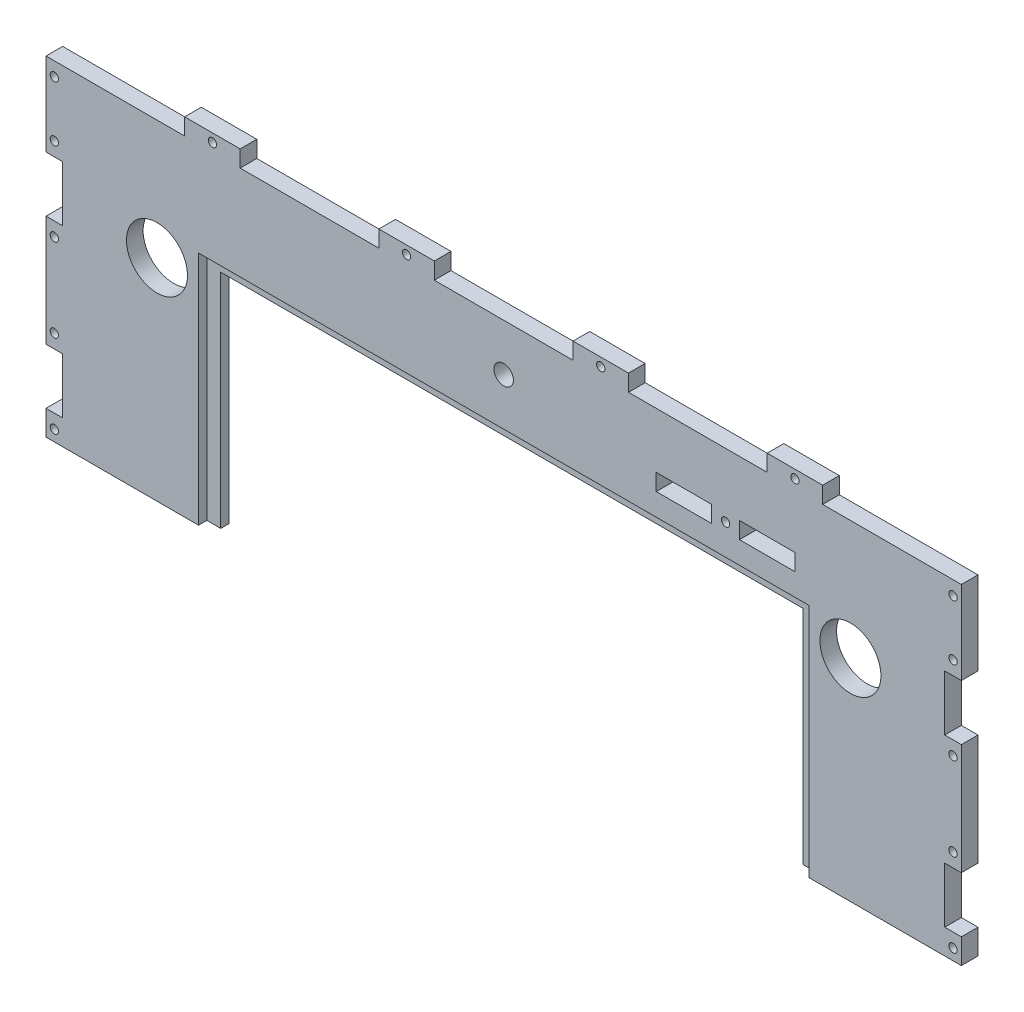
SolidWorks part; units mm, degrees
ref_plane "Plan de face" through (0, 0, 0) normal (0, 0, 1) x (1, 0, 0)
ref_plane "Plan de dessus" through (0, 0, 0) normal (0, 1, 0) x (1, 0, 0)
ref_plane "Plan de droite" through (0, 0, 0) normal (1, 0, 0) x (0, 0, -1)
sketch "Esquisse1" plane through (0, 0, 0) normal (0, 0, 1) x (1, 0, 0)
  line L0 (97.3951, 0) -> (-118.5049, 0) construction
  line L1 (-165, 119) -> (165, 119)
  line L2 (-165, 119) -> (-165, -119)
  line L3 (-165, -119) -> (165, -119)
  line L4 (165, 119) -> (165, -119)
  line L5 (0, 79.3588) -> (0, -79.3588) construction
  line L6 (-92.5, -55) -> (-77.5, -55)
  line L7 (-92.5, -55) -> (-92.5, -61)
  line L8 (-92.5, -61) -> (-77.5, -61)
  line L9 (-77.5, -55) -> (-77.5, -61)
  line L10 (-7.5, -55) -> (7.5, -55)
  line L11 (-7.5, -55) -> (-7.5, -61)
  line L12 (-7.5, -61) -> (7.5, -61)
  line L13 (7.5, -55) -> (7.5, -61)
  line L14 (77.5, -55) -> (92.5, -55)
  line L15 (77.5, -55) -> (77.5, -61)
  line L16 (77.5, -61) -> (92.5, -61)
  line L17 (92.5, -55) -> (92.5, -61)
  line L18 (-225.3679, 76) -> (203.1013, 76) construction
  line L19 (55, 99) -> (75, 99)
  line L20 (55, 99) -> (55, 93)
  line L21 (55, 93) -> (75, 93)
  line L22 (75, 99) -> (75, 93)
  line L23 (85, 99) -> (105, 99)
  line L24 (85, 99) -> (85, 93)
  line L25 (85, 93) -> (105, 93)
  line L26 (105, 99) -> (105, 93)
  circle A0 centre (-125, 76) radius 11
  circle A1 centre (125, 76) radius 11
  dimension "D23" = 22
  dimension "D24" = 22
  dimension "D1" = 238
  dimension "D2" = 330
  dimension "D3" = 165
  dimension "D4" = 119
  dimension "D5" = 15
  dimension "D6" = 6
  dimension "D7" = 6
  dimension "D8" = 15
  dimension "D9" = 6
  dimension "D10" = 15
  dimension "D11" = 70
  dimension "D12" = 70
  dimension "D13" = 58
  dimension "D14" = 72.5
  dimension "D15" = 6
  dimension "D16" = 20
  dimension "D17" = 20
  dimension "D18" = 6
  dimension "D19" = 10
  dimension "D20" = 60
  dimension "D21" = 20
  dimension "D22" = 20
  dimension "D25" = 40
  dimension "D26" = 40
  dimension "D27" = 195
extrude "Boss.-Extru.1" add sketch "Esquisse1" along normal blind 6
sketch "Esquisse2" plane through (0, 0, 6) normal (0, 0, 1) x (1, 0, 0)
  line L0 (243.146, 0) -> (-260.0003, 0) construction
  line L1 (0, 180.4713) -> (0, -129.6072) construction
  line L2 (165, 119) -> (-165, 119) construction
  line L3 (-115, 119) -> (-95, 119)
  line L4 (-115, 119) -> (-115, 125)
  line L5 (-115, 125) -> (-95, 125)
  line L6 (-95, 119) -> (-95, 125)
  line L7 (-165, 119) -> (-165, -119) construction
  line L8 (-45, 119) -> (-25, 119)
  line L9 (-45, 119) -> (-45, 125)
  line L10 (-45, 125) -> (-25, 125)
  line L11 (-25, 119) -> (-25, 125)
  line L12 (25, 119) -> (25, 125)
  line L13 (45, 125) -> (25, 125)
  line L14 (45, 119) -> (45, 125)
  line L15 (45, 119) -> (25, 119)
  line L16 (95, 119) -> (95, 125)
  line L17 (115, 125) -> (95, 125)
  line L18 (115, 119) -> (115, 125)
  line L19 (115, 119) -> (95, 119)
  line L20 (-115, 119) -> (-95, 119)
  line L21 (-115, 119) -> (-115, 125)
  line L22 (-115, 125) -> (-95, 125)
  line L23 (-95, 119) -> (-95, 125)
  line L24 (-45, 119) -> (-25, 119)
  line L25 (-45, 119) -> (-45, 125)
  line L26 (-45, 125) -> (-25, 125)
  line L27 (-25, 119) -> (-25, 125)
  line L28 (25, 119) -> (25, 125)
  line L29 (45, 125) -> (25, 125)
  line L30 (45, 119) -> (45, 125)
  line L31 (45, 119) -> (25, 119)
  line L32 (95, 119) -> (95, 125)
  line L33 (115, 125) -> (95, 125)
  line L34 (115, 119) -> (115, 125)
  line L35 (115, 119) -> (95, 119)
  line L36 (115, -119) -> (95, -119)
  line L37 (115, -119) -> (115, -125)
  line L38 (115, -125) -> (95, -125)
  line L39 (95, -119) -> (95, -125)
  line L40 (45, -119) -> (25, -119)
  line L41 (45, -119) -> (45, -125)
  line L42 (45, -125) -> (25, -125)
  line L43 (25, -119) -> (25, -125)
  line L44 (-25, -119) -> (-25, -125)
  line L45 (-45, -125) -> (-25, -125)
  line L46 (-45, -119) -> (-45, -125)
  line L47 (-45, -119) -> (-25, -119)
  line L48 (-95, -119) -> (-95, -125)
  line L49 (-115, -125) -> (-95, -125)
  line L50 (-115, -119) -> (-115, -125)
  line L51 (-115, -119) -> (-95, -119)
  line L52 (115, -119) -> (95, -119)
  line L53 (115, -119) -> (115, -125)
  line L54 (115, -125) -> (95, -125)
  line L55 (95, -119) -> (95, -125)
  line L56 (45, -119) -> (25, -119)
  line L57 (45, -119) -> (45, -125)
  line L58 (45, -125) -> (25, -125)
  line L59 (25, -119) -> (25, -125)
  line L60 (-25, -119) -> (-25, -125)
  line L61 (-45, -125) -> (-25, -125)
  line L62 (-45, -119) -> (-45, -125)
  line L63 (-45, -119) -> (-25, -119)
  line L64 (-95, -119) -> (-95, -125)
  line L65 (-115, -125) -> (-95, -125)
  line L66 (-115, -119) -> (-115, -125)
  line L67 (-115, -119) -> (-95, -119)
  line M9 (-165, -119) -> (165, -119)
  line M11 (165, 119) -> (-165, 119)
  dimension "D1" = 6
  dimension "D2" = 6
  dimension "D3" = 20
  dimension "D4" = 20
  dimension "D5" = 50
  dimension "D6" = 50
extrude "Boss.-Extru.2" add sketch "Esquisse2" against normal blind 6 contours L6 L5 L4 M11 | L11 L10 L9 M11 | L14 L13 L12 M11 | L18 L17 L16 M11 | L39 L38 L37 M9 | L43 L42 L41 M9 | L46 L45 L44 M9 | L50 L49 L48 M9
sketch "Esquisse3" plane through (0, 0, 6) normal (0, 0, 1) x (1, 0, 0)
  line L0 (-165, 119) -> (-165, -119) construction
  line L1 (-165, 69) -> (-159, 69)
  line L2 (-165, 69) -> (-165, 89)
  line L3 (-165, 89) -> (-159, 89)
  line L4 (-159, 69) -> (-159, 89)
  line L5 (234.1368, 0) -> (-337.9213, 0) construction
  line L6 (-165, 29) -> (-159, 29)
  line L7 (-165, 29) -> (-165, 9)
  line L8 (-165, 9) -> (-159, 9)
  line L9 (-159, 29) -> (-159, 9)
  line L10 (0, 279.7488) -> (0, -188.1201) construction
  line L11 (-115, 119) -> (-165, 119) construction
  line L12 (-159, -29) -> (-159, -9)
  line L13 (-165, -9) -> (-159, -9)
  line L14 (-165, -29) -> (-165, -9)
  line L15 (-165, -29) -> (-159, -29)
  line L16 (-159, -69) -> (-159, -89)
  line L17 (-165, -89) -> (-159, -89)
  line L18 (-165, -69) -> (-165, -89)
  line L19 (-165, -69) -> (-159, -69)
  line L20 (165, -69) -> (159, -69)
  line L21 (165, -69) -> (165, -89)
  line L22 (165, -89) -> (159, -89)
  line L23 (159, -69) -> (159, -89)
  line L24 (165, -29) -> (159, -29)
  line L25 (165, -29) -> (165, -9)
  line L26 (165, -9) -> (159, -9)
  line L27 (159, -29) -> (159, -9)
  line L28 (159, 29) -> (159, 9)
  line L29 (165, 9) -> (159, 9)
  line L30 (165, 29) -> (165, 9)
  line L31 (165, 29) -> (159, 29)
  line L32 (159, 69) -> (159, 89)
  line L33 (165, 89) -> (159, 89)
  line L34 (165, 69) -> (165, 89)
  line L35 (165, 69) -> (159, 69)
  line L36 (153, -119) -> (153, -109)
  line L37 (-165, -119) -> (-153, -119)
  line L38 (-165, -119) -> (-165, -109)
  line L39 (-165, -109) -> (-153, -109)
  line L40 (-153, -119) -> (-153, -109)
  line L41 (165, -109) -> (153, -109)
  line L42 (165, -119) -> (165, -109)
  line L43 (165, -119) -> (153, -119)
  dimension "D1" = 40
  dimension "D2" = 6
  dimension "D3" = 6
  dimension "D4" = 20
  dimension "D5" = 20
  dimension "D6" = 30
  dimension "D7" = 12
  dimension "D8" = 10
extrude "Enlèv. mat.-Extru.1" cut sketch "Esquisse3" against normal blind 6
sketch "Esquisse4" plane through (0, 0, 6) normal (0, 0, 1) x (1, 0, 0)
  line L0 (-162, 122) -> (-162, -131.0602) construction
  line L1 (0, 158.5579) -> (0, -182.4489) construction
  line L2 (-115, 119) -> (-165, 119) construction
  line L3 (-106.4439, -58) -> (117.3944, -58) construction
  line L4 (-159, 89) -> (-165, 89) construction
  line L5 (-165, 119) -> (-165, 89) construction
  line L6 (-165, 69) -> (-159, 69) construction
  line L7 (-159, 29) -> (-165, 29) construction
  line L8 (-165, 9) -> (-159, 9) construction
  line L9 (-159, -9) -> (-165, -9) construction
  line L10 (-92.5, -55) -> (-92.5, -61) construction
  line L11 (-77.5, -61) -> (-77.5, -55) construction
  line L12 (-165, -29) -> (-159, -29) construction
  line L13 (-159, -69) -> (-165, -69) construction
  line L14 (-165, -89) -> (-159, -89) construction
  line L15 (-7.5, -55) -> (-7.5, -61) construction
  line L16 (162, 122) -> (162, -131.0602) construction
  line L17 (116.5184, 96) -> (43.4816, 96) construction
  line L18 (-126.5544, 122) -> (2.7821, 122) construction
  line L19 (-45, 119) -> (-95, 119) construction
  line L20 (-45, 119) -> (-45, 125) construction
  line L21 (75, 93) -> (75, 99) construction
  line L23 (55, 93) -> (75, 93) construction
  circle A0 centre (-162, 114) radius 1.5
  circle A1 centre (-162, 94) radius 1.5
  circle A2 centre (-162, 64) radius 1.5
  circle A3 centre (-162, 34) radius 1.5
  circle A4 centre (-162, 4) radius 1.5
  circle A5 centre (-105, 122) radius 1.5
  circle A6 centre (-162, -4) radius 1.5
  circle A7 centre (-162, -34) radius 1.5
  circle A8 centre (-162, -64) radius 1.5
  circle A9 centre (-162, -94) radius 1.5
  circle A10 centre (-97.5, -58) radius 1.5
  circle A11 centre (-72.5, -58) radius 1.5
  circle A12 centre (162, -94) radius 1.5
  circle A13 centre (162, -64) radius 1.5
  circle A14 centre (162, -34) radius 1.5
  circle A15 centre (162, -4) radius 1.5
  circle A16 centre (80, 96) radius 1.5
  circle A17 centre (162, 4) radius 1.5
  circle A18 centre (162, 34) radius 1.5
  circle A19 centre (162, 64) radius 1.5
  circle A20 centre (162, 94) radius 1.5
  circle A21 centre (162, 114) radius 1.5
  circle A22 centre (-12.5, -58) radius 1.5
  circle A23 centre (12.5, -58) radius 1.5
  circle A24 centre (72.5, -58) radius 1.5
  circle A25 centre (97.5, -58) radius 1.5
  circle A26 centre (-35, 122) radius 1.5
  circle A27 centre (35, 122) radius 1.5
  circle A28 centre (105, 122) radius 1.5
  dimension "D1" = 3
  dimension "D2" = 3
  dimension "D3" = 3
  dimension "D4" = 3
  dimension "D5" = 3
  dimension "D6" = 3
  dimension "D7" = 3
  dimension "D8" = 3
  dimension "D9" = 3
  dimension "D10" = 3
  dimension "D11" = 3
  dimension "D12" = 5
  dimension "D13" = 5
  dimension "D15" = 5
  dimension "D16" = 5
  dimension "D17" = 5
  dimension "D19" = 3
  dimension "D20" = 5
  dimension "D21" = 5
  dimension "D23" = 3
  dimension "D24" = 3
  dimension "D25" = 5
  dimension "D26" = 5
  dimension "D27" = 5
  dimension "D28" = 10
  dimension "D29" = 3
  dimension "D30" = 5
  dimension "D31" = 3
  dimension "D33" = 10
  dimension "D14" = 3
  dimension "D18" = 5
  dimension "D22" = 5
  dimension "D32" = 3
extrude "Enlèv. mat.-Extru.2" cut sketch "Esquisse4" against normal blind 6
sketch "Esquisse5" plane through (0, 0, 6) normal (0, 0, 1) x (1, 0, 0)
  line L1 (-200.0968, 0) -> (223.5072, 0)
  line L2 (-200.0968, 0) -> (-200.0968, -150.3561)
  line L3 (-200.0968, -150.3561) -> (223.5072, -150.3561)
  line L4 (223.5072, 0) -> (223.5072, -150.3561)
extrude "Enlèv. mat.-Extru.3" cut sketch "Esquisse5" against normal blind 6
sketch "Esquisse6" plane through (0, 0, 6) normal (0, 0, 1) x (1, 0, 0)
  line L0 (-165, 69) -> (-165, 29) construction
  line L2 (165, 0) -> (-165, 0) construction
  text T0 "SUDRIABOTIK" font "Century Gothic" height in points 72
  dimension "D1" = 83.5
  dimension "D2" = 29.5
extrude "Enlèv. mat.-Extru.4" cut sketch "Esquisse6" against normal blind 6
sketch "Esquisse7" plane through (0, 0, 6) normal (0, 0, 1) x (1, 0, 0)
  line L0 (-42.8696, 29.5) -> (-48.7731, 29.5) construction
  line L1 (-44.3875, 29.5) -> (-45.9701, 29.5)
  line L2 (-44.3875, 29.5) -> (-44.3875, 31.4538)
  line L3 (-44.3875, 31.4538) -> (-45.9701, 31.4538)
  line L4 (-45.9701, 29.5) -> (-45.9701, 31.4538)
  line L5 (-47.0635, 31.4538) -> (-44.8768, 31.4538) construction
  line L6 (-23.9531, 46.5962) -> (-27.525, 46.5962) construction
  line L7 (-45.1788, 46.5937) -> (-43.5909, 46.5937)
  line L8 (-45.1788, 46.5937) -> (-45.1788, 48.5305)
  line L9 (-45.1788, 48.5305) -> (-43.5909, 48.5305)
  line L10 (-43.5909, 46.5937) -> (-43.5909, 48.5305)
  line L11 (-26.3286, 46.5962) -> (-25.4223, 46.5962)
  line L12 (-26.3286, 46.5962) -> (-26.3286, 48.55)
  line L13 (-26.3286, 48.55) -> (-25.4223, 48.55)
  line L14 (-25.4223, 46.5962) -> (-25.4223, 48.55)
  line L15 (-27.525, 46.5962) -> (-27.525, 40.2462) construction
  line L16 (-27.525, 43.4212) -> (-29.2346, 43.4212)
  line L17 (-27.525, 43.4212) -> (-27.525, 42.4505)
  line L18 (-27.525, 42.4505) -> (-29.2346, 42.4505)
  line L19 (-29.2346, 43.4212) -> (-29.2346, 42.4505)
  line L20 (-29.2346, 29.5) -> (-29.2346, 48.55) construction
  line L21 (-2.2967, 37.5596) -> (4.5112, 37.5596) construction
  line L22 (0.6712, 37.5596) -> (1.8879, 37.5596)
  line L23 (0.6712, 37.5596) -> (0.6712, 35.6058)
  line L24 (0.6712, 35.6058) -> (1.8879, 35.6058)
  line L25 (1.8879, 37.5596) -> (1.8879, 35.6058)
  line L26 (5.4118, 35.6058) -> (-3.224, 35.6058) construction
  line L27 (15.2154, 46.5962) -> (15.2154, 40.4904) construction
  line L28 (15.2154, 43.5433) -> (13.5058, 43.5433)
  line L29 (15.2154, 43.5433) -> (15.2154, 40.4904)
  line L30 (15.2154, 40.4904) -> (13.5058, 40.4904)
  line L31 (13.5058, 43.5433) -> (13.5058, 40.4904)
  line L32 (13.5058, 29.5) -> (13.5058, 48.55) construction
  line L33 (15.2154, 38.5365) -> (15.2154, 31.4538) construction
  line L34 (15.2154, 32.964) -> (13.5058, 32.964)
  line L35 (15.2154, 32.964) -> (15.2154, 35.6058)
  line L36 (15.2154, 35.6058) -> (13.5058, 35.6058)
  line L37 (13.5058, 32.964) -> (13.5058, 35.6058)
  line L39 (29.3929, 39.4529) -> (27.6822, 39.4529)
  line L40 (29.3929, 39.4529) -> (29.3929, 38.5462)
  line L41 (29.3929, 38.5462) -> (27.6822, 38.5462)
  line L42 (27.6822, 39.4529) -> (27.6822, 38.5462)
  line L43 (45.9733, 39.5873) -> (47.6814, 39.5873)
  line L44 (45.9733, 39.5873) -> (45.9733, 38.4818)
  line L45 (45.9733, 38.4818) -> (47.6814, 38.4818)
  line L46 (47.6814, 39.5873) -> (47.6814, 38.4818)
  spline S0 degree 3 poles (-39.8701, 46.0619) (-40.0299, 46.1061) (-40.3695, 46.2) (-40.9238, 46.3025) (-41.5477, 46.3928) (-42.2438, 46.4694) (-43.0115, 46.5243) (-43.8512, 46.5655) (-44.7634, 46.5933) (-45.3958, 46.5952) (-45.724, 46.5962) knots 0 0 0 0 0.084319 0.179285 0.286583 0.405111 0.535593 0.67819 0.832976 1 1 1 1 construction
  spline S1 degree 3 poles (-44.9264, 48.55) (-44.5919, 48.5476) (-43.9455, 48.5429) (-43.0114, 48.5134) (-42.1472, 48.4612) (-41.3556, 48.3852) (-40.6345, 48.2918) (-39.986, 48.1748) (-39.4066, 48.0366) (-39.0502, 47.9188) (-38.8817, 47.8631) knots 0 0 0 0 0.164289 0.317406 0.458844 0.589367 0.707831 0.81577 0.91288 1 1 1 1 construction
  spline S2 degree 3 poles (37.6465, 47.0846) (37.4657, 47.0824) (37.1058, 47.078) (36.5709, 47.0202) (36.043, 46.9379) (35.522, 46.8204) (35.0101, 46.6604) (34.5026, 46.4762) (34.004, 46.2518) (33.516, 45.9983) (33.0429, 45.7178) (32.5966, 45.4077) (32.1757, 45.0754) (31.7814, 44.72) (31.4148, 44.3398) (31.0687, 43.9406) (30.757, 43.5108) (30.4714, 43.0623) (30.2157, 42.5955) (29.9884, 42.1154) (29.8024, 41.618) (29.6508, 41.1088) (29.5251, 40.5886) (29.4454, 40.0534) (29.387, 39.5058) (29.3829, 39.1358) (29.3808, 38.9487) knots 0 0 0 0 0.042023 0.083645 0.124984 0.166247 0.207702 0.249631 0.291742 0.334743 0.37746 0.419556 0.461044 0.502096 0.542891 0.583801 0.624864 0.666225 0.707399 0.748557 0.789655 0.83074 0.87207 0.913993 0.956498 1 1 1 1 construction
  spline S3 degree 3 poles (37.7151, 29.0115) (37.3699, 29.02) (36.6894, 29.0366) (35.6905, 29.1791) (34.731, 29.4019) (33.8138, 29.7204) (32.9384, 30.132) (32.1029, 30.6338) (31.3109, 31.2293) (30.5688, 31.9051) (29.8898, 32.6409) (29.2979, 33.4292) (28.7959, 34.2546) (28.3857, 35.1195) (28.0609, 36.0196) (27.8394, 36.9609) (27.6961, 37.9381) (27.6795, 38.6034) (27.6712, 38.941) knots 0 0 0 0 0.065819 0.129747 0.192072 0.253459 0.31457 0.37628 0.439026 0.503267 0.567493 0.629705 0.691 0.751452 0.812004 0.87315 0.935635 1 1 1 1 construction
  spline S4 degree 3 poles (45.9885, 39.0364) (45.9863, 39.221) (45.9819, 39.5872) (45.9246, 40.1286) (45.8424, 40.6579) (45.7239, 41.1732) (45.5713, 41.6744) (45.383, 42.1613) (45.161, 42.6355) (44.9062, 43.0959) (44.6199, 43.5378) (44.3069, 43.9601) (43.962, 44.3551) (43.595, 44.7325) (43.1968, 45.0842) (42.7691, 45.4104) (42.3171, 45.7188) (41.8385, 45.9971) (41.3446, 46.2541) (40.8378, 46.4743) (40.3238, 46.6613) (39.804, 46.8209) (39.274, 46.9374) (38.7373, 47.0203) (38.1947, 47.078) (37.8298, 47.0824) (37.6465, 47.0846) knots 0 0 0 0 0.042915 0.08513 0.126473 0.167453 0.207976 0.248249 0.28875 0.32967 0.370537 0.411129 0.451819 0.492406 0.533486 0.575263 0.617441 0.660672 0.70394 0.746868 0.789079 0.831104 0.873238 0.915166 0.957381 1 1 1 1 construction
  spline S5 degree 3 poles (47.6981, 39.0326) (47.6896, 38.69) (47.673, 38.0145) (47.5306, 37.0231) (47.3072, 36.0702) (46.9883, 35.1571) (46.5788, 34.2831) (46.0745, 33.4504) (45.4805, 32.6588) (44.8044, 31.9169) (44.0675, 31.2365) (43.277, 30.6437) (42.4508, 30.1336) (41.5783, 29.7265) (40.6709, 29.4012) (39.7207, 29.1794) (38.732, 29.0363) (38.0578, 29.0199) (37.7151, 29.0115) knots 0 0 0 0 0.065227 0.128569 0.19032 0.251378 0.312388 0.373789 0.436431 0.500567 0.564687 0.627136 0.688455 0.749246 0.810155 0.871671 0.934773 1 1 1 1 construction
  spline S6 degree 3 poles (29.3808, 38.9487) (29.3877, 38.6735) (29.4014, 38.1321) (29.5209, 37.3387) (29.705, 36.5762) (29.9763, 35.8488) (30.3157, 35.1502) (30.7349, 34.4867) (31.2316, 33.858) (31.7959, 33.2686) (32.4127, 32.7306) (33.0676, 32.2584) (33.7537, 31.8588) (34.4727, 31.5333) (35.2208, 31.2753) (36.0029, 31.0986) (36.8136, 30.9822) (37.3662, 30.9711) (37.6465, 30.9654) knots 0 0 0 0 0.064504 0.126899 0.187747 0.24815 0.308586 0.369583 0.431827 0.49618 0.560668 0.623504 0.68526 0.746537 0.808327 0.870486 0.934317 1 1 1 1 construction
  spline S7 degree 3 poles (37.6465, 30.9654) (37.8348, 30.968) (38.2084, 30.9731) (38.7641, 31.0248) (39.3098, 31.1077) (39.8447, 31.2271) (40.3682, 31.3765) (40.8825, 31.5539) (41.3822, 31.7754) (41.8735, 32.02) (42.3437, 32.2989) (42.7926, 32.5985) (43.2089, 32.9303) (43.6029, 33.2804) (43.9709, 33.6557) (44.3106, 34.0559) (44.6208, 34.4834) (44.9063, 34.9313) (45.1611, 35.3993) (45.383, 35.8812) (45.5713, 36.3756) (45.7233, 36.8834) (45.8425, 37.4035) (45.9245, 37.9367) (45.982, 38.4819) (45.9863, 38.8506) (45.9885, 39.0364) knots 0 0 0 0 0.043633 0.086538 0.129177 0.171436 0.213416 0.255266 0.297369 0.339941 0.382347 0.423953 0.464871 0.505572 0.546003 0.586568 0.627065 0.668271 0.709549 0.750428 0.791096 0.832027 0.873136 0.914611 0.956956 1 1 1 1 construction
extrude "Boss.-Extru.5" add sketch "Esquisse7" against normal blind 6
sketch "Esquisse8" plane through (0, 0, 6) normal (0, 0, 1) x (1, 0, 0)
  line L0 (165, 0) -> (-165, 0) construction
  line L1 (-105.0044, 0) -> (104.9956, 0)
  line L2 (-105.0044, 0) -> (-105.0044, 80)
  line L3 (-105.0044, 80) -> (104.9956, 80)
  line L4 (104.9956, 0) -> (104.9956, 80)
  dimension "D1" = 210
  dimension "D2" = 80
  dimension "D3" = 23.96
extrude "Enlèv. mat.-Extru.5" cut sketch "Esquisse8" against normal blind 6 contours L2 L3 L4 L1
sketch "Esquisse11" plane through (0, 0, 6) normal (0, 0, 1) x (1, 0, 0)
  line L0 (-110.0044, 0) -> (-110.0044, 85)
  line L1 (-105.0044, 0) -> (-165, 0) construction
  line L2 (-110.0044, 85) -> (109.9956, 85)
  line L3 (109.9956, 85) -> (109.9956, 0)
  line L4 (165, 0) -> (104.9956, 0) construction
  line L5 (-105.0044, 0) -> (-105.0044, 80) construction
  line L6 (-105.0044, 80) -> (104.9956, 80) construction
  line L7 (104.9956, 0) -> (104.9956, 80) construction
  dimension "D1" = 5
  dimension "D2" = 5
  dimension "D3" = 5
extrude "Enlèv. mat.-Extru.7" cut sketch "Esquisse11" against normal blind 3 and the other way through all flip side to cut
sketch "Esquisse12" plane through (0, 0, 6) normal (0, 0, 1) x (1, 0, 0)
  line L0 (25, 119) -> (-25, 119) construction
  line L2 (-165, 119) -> (-165, 89) construction
  circle A0 centre (0, 102) radius 3.5
  dimension "D1" = 17
  dimension "D2" = 165
extrude "Enlèv. mat.-Extru.8" cut sketch "Esquisse12" against normal blind 10
equation "\"D3@Esquisse1\"=\"D2@Esquisse1\"/2"
equation "\"D4@Esquisse1\"=\"D1@Esquisse1\"/2"
